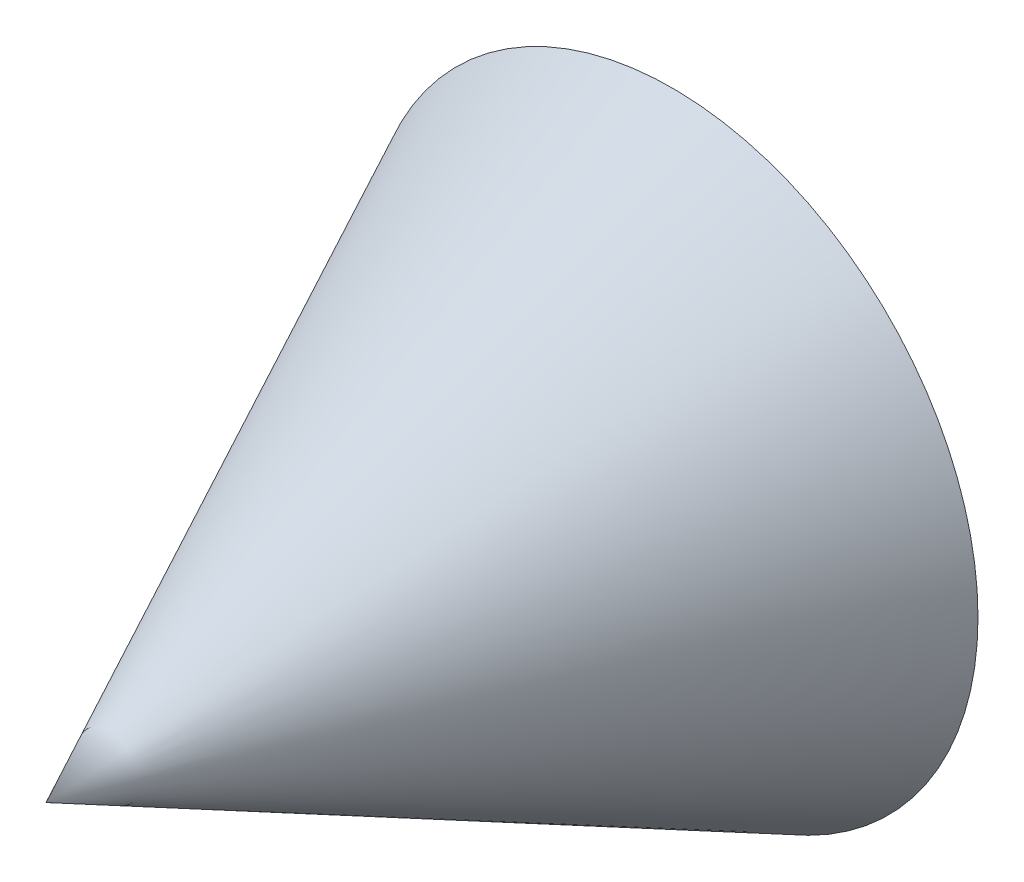
SolidWorks part; units mm, degrees
ref_plane "Plan de face" through (0, 0, 0) normal (0, 0, 1) x (1, 0, 0)
ref_plane "Plan de dessus" through (0, 0, 0) normal (0, 1, 0) x (1, 0, 0)
ref_plane "Plan de droite" through (0, 0, 0) normal (1, 0, 0) x (0, 0, -1)
sketch "Esquisse1" plane through (0, 0, 0) normal (0, 0, 1) x (1, 0, 0)
  circle A0 centre (0, 0) radius 40
extrude "Boss.-Extru.1" add sketch "Esquisse1" along normal blind 83 draft 26
sketch "Esquisse2" plane through (0, 0, 0) normal (0, 0, -1) x (-1, 0, 0)
  circle A0 centre (0, 0) radius 30
extrude "Enlèv. mat.-Extru.1" cut sketch "Esquisse2" against normal blind 53 draft 30
